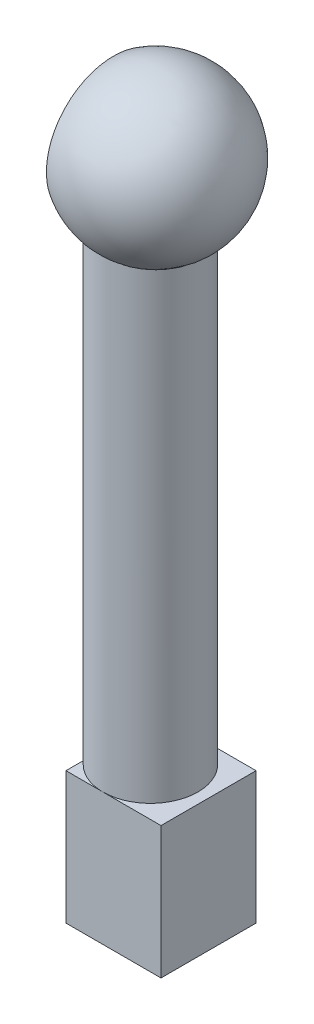
SolidWorks part; units mm, degrees
ref_plane "Спереди" through (0, 0, 0) normal (0, 0, 1) x (1, 0, 0)
ref_plane "Сверху" through (0, 0, 0) normal (0, 1, 0) x (1, 0, 0)
ref_plane "Справа" through (0, 0, 0) normal (1, 0, 0) x (0, 0, -1)
sketch "Sketch1" plane through (0, 0, 0) normal (1, 0, 0) x (0, 0, -1)
  line L1 (9, -12.5) -> (-9, -12.5)
  line L2 (9, -12.5) -> (9, 12.5)
  line L3 (9, 12.5) -> (-9, 12.5)
  line L4 (-9, -12.5) -> (-9, 12.5)
  line L5 (9, -12.5) -> (-9, 12.5) construction
  line L6 (9, 12.5) -> (-9, -12.5) construction
  point P0 (0, 0)
  dimension "D1" = 18
  dimension "D2" = 25
extrude "Boss-Extrude1" add sketch "Sketch1" along normal blind 18
sketch "Sketch2" plane through (0, -12.5, 0) normal (0, -1, 0) x (1, 0, 0)
  line L0 (12, 9) -> (12, -9) construction
  line L3 (18, 9) -> (0, 9) construction
  line L4 (8.5, -6.2) -> (15.5, -6.2)
  line L5 (8.5, -6.2) -> (8.5, 6.2)
  line L6 (8.5, 6.2) -> (15.5, 6.2)
  line L7 (15.5, -6.2) -> (15.5, 6.2)
  line L8 (8.5, -6.2) -> (15.5, 6.2) construction
  line L9 (8.5, 6.2) -> (15.5, -6.2) construction
  line L10 (18, -9) -> (0, -9) construction
  point P2 (0, 0)
  point P3 (5.1301, 7.7933)
  point P6 (12, 0)
  point P11 (0, 0)
  point P12 (5.7562, -6.463)
  dimension "D1" = 7
  dimension "D2" = 12.4
  dimension "D3" = 6
extrude "Cut-Extrude1" cut sketch "Sketch2" against normal blind 20
sketch "Sketch3" plane through (0, 12.5, 0) normal (0, 1, 0) x (1, 0, 0)
  line L0 (0, 9) -> (0, -9) construction
  line L1 (7, -9) -> (7, 9) construction
  line L2 (18, -9) -> (0, -9) construction
  line L3 (18, 9) -> (0, 9) construction
  line L4 (0, 5.6569) -> (0, -5.6569)
  circle A0 centre (7, 0) radius 9 construction
  arc A1 (0, -5.6569) -> (0, 5.6569) centre (7, 0) ccw
  dimension "D1" = 7
extrude "Boss-Extrude2" add sketch "Sketch3" along normal blind 100
sketch "Sketch6" plane through (0, 112.5, 0) normal (0, 1, 0) x (1, 0, 0)
  line L0 (8, 15) -> (8, -15)
  line L1 (0, 5.6569) -> (0, -5.6569) construction
  line L2 (0, 0) -> (16, 0) construction
  arc A0 (8, -15) -> (8, 15) centre (8, 0) cw
  arc A1 (0, -5.6569) -> (0, 5.6569) centre (7, 0) ccw construction
  point P3 (-7, 0)
  point P4 (8, 0)
  point P12 (0, 0)
  point P13 (0, 0)
  point P14 (0, 0)
  point P15 (8, 0)
  dimension "D1" = 15
revolve "Revolve2" add sketch "Sketch6" angle 360 about L0
sketch "Sketch7" plane through (0, 0, 0) normal (-1, 0, 0) x (0, 0, 1)
  arc A0 (-5.6569, 101.1422) -> (5.6569, 101.1422) centre (0, 152.2794) cw
  arc A1 (-5.6569, 101.1422) -> (5.6569, 101.1422) centre (0, 112.5) ccw
extrude "Cut-Extrude2" cut sketch "Sketch7" along normal blind 100
